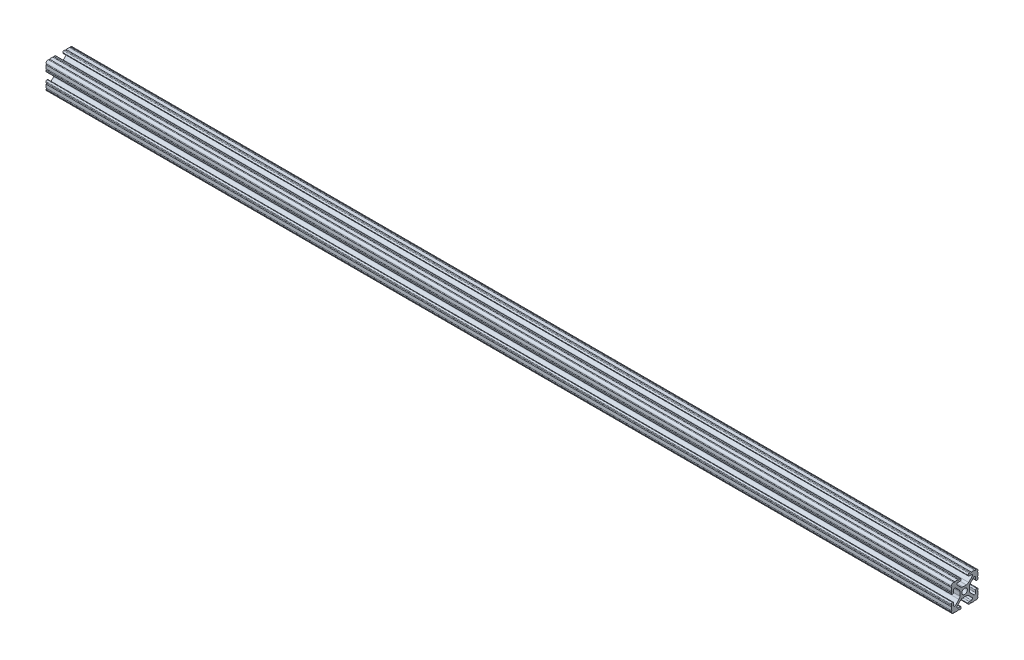
SolidWorks part; units mm, degrees
ref_plane "Front Plane" through (0, 0, 0) normal (0, 0, 1) x (1, 0, 0)
ref_plane "Top Plane" through (0, 0, 0) normal (0, 1, 0) x (1, 0, 0)
ref_plane "Right Plane" through (0, 0, 0) normal (1, 0, 0) x (0, 0, -1)
sketch "Sketch1" plane through (0, 0, 0) normal (0, 0, 1) x (1, 0, 0)
  line L0 (0, 0) -> (860, 0)
  dimension "D1" = 860
other "Extrusion 1010 PROFILE(1)"
ref_plane "Plane1" through (0, 0, 0) normal (1, 0, 0) x (0, 1, 0)
sketch "Sketch16" plane through (0, 0, 0) normal (1, 0, 0) x (0, 1, 0)
  line L1 (12.7, 12.7) -> (-12.7, 12.7) construction
  line L2 (12.7, 12.7) -> (12.7, -12.7) construction
  line L3 (12.7, -12.7) -> (-12.7, -12.7) construction
  line L4 (-12.7, 12.7) -> (-12.7, -12.7) construction
  line L5 (12.7, 12.7) -> (-12.7, -12.7) construction
  line L6 (12.7, -12.7) -> (-12.7, 12.7) construction
  line L88 (-1.7093, -4.4958) -> (1.7093, -4.4958)
  line L89 (3.9523, -5.4237) -> (7.1797, -8.6452)
  line L90 (6.4164, -10.4902) -> (4.2875, -10.4902)
  line L91 (3.2385, -11.5392) -> (3.2385, -11.651)
  line L92 (4.2875, -12.7) -> (5.3171, -12.7)
  line L93 (6.3331, -12.7) -> (9.5504, -12.7)
  line L94 (12.7, -9.5504) -> (12.7, -6.3331)
  line L95 (12.7, -5.3171) -> (12.7, -4.2875)
  line L96 (11.651, -3.2385) -> (11.5392, -3.2385)
  line L97 (10.4902, -4.2875) -> (10.4902, -6.4021)
  line L98 (8.737, -7.1292) -> (5.4405, -3.8388)
  line L99 (4.5085, -1.5917) -> (4.5085, 1.5917)
  line L100 (5.4405, 3.8388) -> (8.737, 7.1292)
  line L101 (10.4902, 6.4021) -> (10.4902, 4.2875)
  line L102 (11.5392, 3.2385) -> (11.651, 3.2385)
  line L103 (12.7, 4.2875) -> (12.7, 5.3171)
  line L104 (12.7, 6.3331) -> (12.7, 9.5504)
  line L105 (9.5504, 12.7) -> (6.3331, 12.7)
  line L106 (5.3171, 12.7) -> (4.2875, 12.7)
  line L107 (3.2384, 11.651) -> (3.2384, 11.5392)
  line L108 (4.2875, 10.4902) -> (6.4768, 10.4902)
  line L109 (7.2072, 8.7245) -> (3.9003, 5.4237)
  line L110 (1.6573, 4.4958) -> (-1.6573, 4.4958)
  line L111 (-3.9003, 5.4237) -> (-7.2072, 8.7245)
  line L112 (-6.4768, 10.4902) -> (-4.2875, 10.4902)
  line L113 (-3.2384, 11.5392) -> (-3.2384, 11.651)
  line L114 (-4.2875, 12.7) -> (-5.3171, 12.7)
  line L115 (-6.3331, 12.7) -> (-9.5504, 12.7)
  line L116 (-12.7, 9.5504) -> (-12.7, 6.3331)
  line L117 (-12.7, 5.3171) -> (-12.7, 4.2875)
  line L118 (-11.651, 3.2385) -> (-11.5392, 3.2385)
  line L119 (-10.4902, 4.2875) -> (-10.4902, 6.4021)
  line L120 (-8.737, 7.1292) -> (-5.4405, 3.8388)
  line L121 (-4.5085, 1.5917) -> (-4.5085, -1.5917)
  line L122 (-5.4405, -3.8388) -> (-8.737, -7.1292)
  line L123 (-10.4902, -6.4021) -> (-10.4902, -4.2875)
  line L124 (-11.5392, -3.2385) -> (-11.651, -3.2385)
  line L125 (-12.7, -4.2875) -> (-12.7, -5.3171)
  line L126 (-12.7, -6.3331) -> (-12.7, -9.5504)
  line L127 (-9.5504, -12.7) -> (-6.3331, -12.7)
  line L128 (-5.3171, -12.7) -> (-4.2875, -12.7)
  line L129 (-3.2385, -11.651) -> (-3.2385, -11.5392)
  line L130 (-4.2875, -10.4902) -> (-6.4164, -10.4902)
  line L131 (-7.1797, -8.6452) -> (-3.9523, -5.4237)
  circle A1 centre (0, 0) radius 2.6035
  arc A104 (-1.7093, -4.4958) -> (-3.9523, -5.4237) centre (-1.7093, -7.6708) ccw
  arc A105 (3.9523, -5.4237) -> (1.7093, -4.4958) centre (1.7093, -7.6708) ccw
  arc A106 (6.4164, -10.4902) -> (7.1797, -8.6452) centre (6.4164, -9.4098) ccw
  arc A107 (4.2875, -10.4902) -> (3.2385, -11.5392) centre (4.2875, -11.5392) ccw
  arc A108 (3.2385, -11.651) -> (4.2875, -12.7) centre (4.2875, -11.651) ccw
  arc A109 (6.3331, -12.7) -> (5.3171, -12.7) centre (5.8251, -12.7) ccw
  arc A110 (10.5664, -12.6998) -> (9.5504, -12.7) centre (10.0584, -12.7) ccw
  arc A111 (10.5664, -12.6998) -> (12.6998, -10.5664) centre (10.5918, -10.5918) ccw
  arc A112 (12.7, -9.5504) -> (12.6998, -10.5664) centre (12.7, -10.0584) ccw
  arc A113 (12.7, -5.3171) -> (12.7, -6.3331) centre (12.7, -5.8251) ccw
  arc A114 (12.7, -4.2875) -> (11.651, -3.2385) centre (11.651, -4.2875) ccw
  arc A115 (11.5392, -3.2385) -> (10.4902, -4.2875) centre (11.5392, -4.2875) ccw
  arc A116 (8.737, -7.1292) -> (10.4902, -6.4021) centre (9.4628, -6.4021) ccw
  arc A117 (4.5085, -1.5917) -> (5.4405, -3.8388) centre (7.6835, -1.5917) ccw
  arc A118 (5.4405, 3.8388) -> (4.5085, 1.5917) centre (7.6835, 1.5917) ccw
  arc A119 (10.4902, 6.4021) -> (8.737, 7.1292) centre (9.4628, 6.4021) ccw
  arc A120 (10.4902, 4.2875) -> (11.5392, 3.2385) centre (11.5392, 4.2875) ccw
  arc A121 (11.651, 3.2385) -> (12.7, 4.2875) centre (11.651, 4.2875) ccw
  arc A122 (12.7, 6.3331) -> (12.7, 5.3171) centre (12.7, 5.8251) ccw
  arc A123 (12.6998, 10.5664) -> (12.7, 9.5504) centre (12.7, 10.0584) ccw
  arc A124 (12.6998, 10.5664) -> (10.5664, 12.6998) centre (10.5918, 10.5918) ccw
  arc A125 (9.5504, 12.7) -> (10.5664, 12.6998) centre (10.0584, 12.7) ccw
  arc A126 (5.3171, 12.7) -> (6.3331, 12.7) centre (5.8251, 12.7) ccw
  arc A127 (4.2875, 12.7) -> (3.2384, 11.651) centre (4.2875, 11.651) ccw
  arc A128 (3.2384, 11.5392) -> (4.2875, 10.4902) centre (4.2875, 11.5392) ccw
  arc A129 (7.2072, 8.7245) -> (6.4768, 10.4902) centre (6.4768, 9.4563) ccw
  arc A130 (1.6573, 4.4958) -> (3.9003, 5.4237) centre (1.6573, 7.6708) ccw
  arc A131 (-3.9003, 5.4237) -> (-1.6573, 4.4958) centre (-1.6573, 7.6708) ccw
  arc A132 (-6.4768, 10.4902) -> (-7.2072, 8.7245) centre (-6.4768, 9.4563) ccw
  arc A133 (-4.2875, 10.4902) -> (-3.2384, 11.5392) centre (-4.2875, 11.5392) ccw
  arc A134 (-3.2384, 11.651) -> (-4.2875, 12.7) centre (-4.2875, 11.651) ccw
  arc A135 (-6.3331, 12.7) -> (-5.3171, 12.7) centre (-5.8251, 12.7) ccw
  arc A136 (-10.5664, 12.6998) -> (-9.5504, 12.7) centre (-10.0584, 12.7) ccw
  arc A137 (-10.5664, 12.6998) -> (-12.6998, 10.5664) centre (-10.5918, 10.5918) ccw
  arc A138 (-12.7, 9.5504) -> (-12.6998, 10.5664) centre (-12.7, 10.0584) ccw
  arc A139 (-12.7, 5.3171) -> (-12.7, 6.3331) centre (-12.7, 5.8251) ccw
  arc A140 (-12.7, 4.2875) -> (-11.651, 3.2385) centre (-11.651, 4.2875) ccw
  arc A141 (-11.5392, 3.2385) -> (-10.4902, 4.2875) centre (-11.5392, 4.2875) ccw
  arc A142 (-8.737, 7.1292) -> (-10.4902, 6.4021) centre (-9.4628, 6.4021) ccw
  arc A143 (-4.5085, 1.5917) -> (-5.4405, 3.8388) centre (-7.6835, 1.5917) ccw
  arc A144 (-5.4405, -3.8388) -> (-4.5085, -1.5917) centre (-7.6835, -1.5917) ccw
  arc A145 (-10.4902, -6.4021) -> (-8.737, -7.1292) centre (-9.4628, -6.4021) ccw
  arc A146 (-10.4902, -4.2875) -> (-11.5392, -3.2385) centre (-11.5392, -4.2875) ccw
  arc A147 (-11.651, -3.2385) -> (-12.7, -4.2875) centre (-11.651, -4.2875) ccw
  arc A148 (-12.7, -6.3331) -> (-12.7, -5.3171) centre (-12.7, -5.8251) ccw
  arc A149 (-12.6998, -10.5664) -> (-12.7, -9.5504) centre (-12.7, -10.0584) ccw
  arc A150 (-12.6998, -10.5664) -> (-10.5664, -12.6998) centre (-10.5918, -10.5918) ccw
  arc A151 (-9.5504, -12.7) -> (-10.5664, -12.6998) centre (-10.0584, -12.7) ccw
  arc A152 (-5.3171, -12.7) -> (-6.3331, -12.7) centre (-5.8251, -12.7) ccw
  arc A153 (-4.2875, -12.7) -> (-3.2385, -11.651) centre (-4.2875, -11.651) ccw
  arc A154 (-3.2385, -11.5392) -> (-4.2875, -10.4902) centre (-4.2875, -11.5392) ccw
  arc A155 (-7.1797, -8.6452) -> (-6.4164, -10.4902) centre (-6.4164, -9.4098) ccw
  point P3 (0, 0)
  point P21 (-12.7, 0)
  point P22 (0, 12.7)
  point P25 (12.7, 0)
  point P28 (0, -12.7)
  point P30 (-12.7, -12.7)
  point P33 (12.7, -12.7)
  point P37 (12.7, 12.7)
  point P40 (-12.7, 12.7)
  point P43 (0, 0)
  dimension "D1" = 25.4
